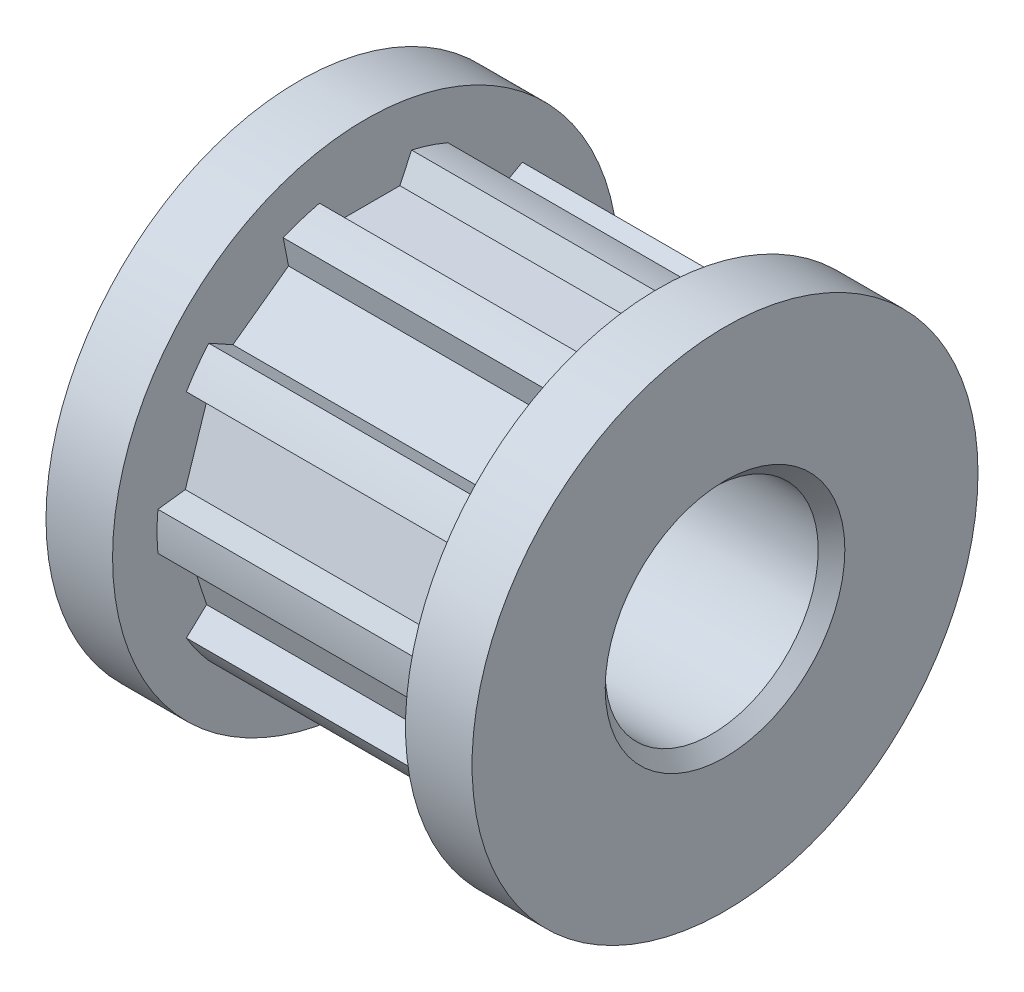
SolidWorks part; units mm, degrees
material "6061 合金"
ref_plane "前视基准面" through (0, 0, 0) normal (0, 0, 1) x (1, 0, 0)
ref_plane "上视基准面" through (0, 0, 0) normal (0, 1, 0) x (1, 0, 0)
ref_plane "右视基准面" through (0, 0, 0) normal (1, 0, 0) x (0, 0, -1)
sketch "草图1" plane through (0, 0, 0) normal (1, 0, 0) x (0, 0, -1)
  line L0 (0, 0) -> (0, 19.2746) construction
  line L22 (0, 0) -> (7.6303, 23.4837) construction
  line L89 (1.7283, 7.6369) -> (1.29, 6.6969)
  line L90 (0, 6.6969) -> (1.29, 6.6969)
  line L91 (3.0906, 7.1942) -> (2.8927, 6.1761)
  line L92 (3.9363, 5.4179) -> (2.8927, 6.1761)
  line L93 (6.729, 4.0037) -> (5.9705, 3.2963)
  line L94 (6.3691, 2.0695) -> (5.9705, 3.2963)
  line L95 (3.9363, 5.4179) -> (4.98, 4.6597)
  line L96 (5.8871, 5.1625) -> (4.98, 4.6597)
  line L97 (7.7972, -0.7162) -> (6.7678, -0.8426)
  line L98 (6.3691, -2.0695) -> (6.7678, -0.8426)
  line L99 (6.3691, 2.0695) -> (6.7678, 0.8426)
  line L100 (7.7972, 0.7162) -> (6.7678, 0.8426)
  line L101 (5.8871, -5.1625) -> (4.98, -4.6597)
  line L102 (3.9363, -5.4179) -> (4.98, -4.6597)
  line L103 (6.3691, -2.0695) -> (5.9705, -3.2963)
  line L104 (6.729, -4.0037) -> (5.9705, -3.2963)
  line L105 (1.7283, -7.6369) -> (1.29, -6.6969)
  line L106 (0, -6.6969) -> (1.29, -6.6969)
  line L107 (3.9363, -5.4179) -> (2.8927, -6.1761)
  line L108 (3.0906, -7.1942) -> (2.8927, -6.1761)
  line L109 (-3.0906, -7.1942) -> (-2.8927, -6.1761)
  line L110 (-3.9363, -5.4179) -> (-2.8927, -6.1761)
  line L111 (0, -6.6969) -> (-1.29, -6.6969)
  line L112 (-1.7283, -7.6369) -> (-1.29, -6.6969)
  line L113 (-6.729, -4.0037) -> (-5.9705, -3.2963)
  line L114 (-6.3691, -2.0695) -> (-5.9705, -3.2963)
  line L115 (-3.9363, -5.4179) -> (-4.98, -4.6597)
  line L116 (-5.8871, -5.1625) -> (-4.98, -4.6597)
  line L117 (-7.7972, 0.7162) -> (-6.7678, 0.8426)
  line L118 (-6.3691, 2.0695) -> (-6.7678, 0.8426)
  line L119 (-6.3691, -2.0695) -> (-6.7678, -0.8426)
  line L120 (-7.7972, -0.7162) -> (-6.7678, -0.8426)
  line L121 (-5.8871, 5.1625) -> (-4.98, 4.6597)
  line L122 (-3.9363, 5.4179) -> (-4.98, 4.6597)
  line L123 (-6.3691, 2.0695) -> (-5.9705, 3.2963)
  line L124 (-6.729, 4.0037) -> (-5.9705, 3.2963)
  line L125 (-1.7283, 7.6369) -> (-1.29, 6.6969)
  line L126 (0, 6.6969) -> (-1.29, 6.6969)
  line L127 (-3.9363, 5.4179) -> (-2.8927, 6.1761)
  line L128 (-3.0906, 7.1942) -> (-2.8927, 6.1761)
  arc A3 (3.0906, 7.1942) -> (1.7283, 7.6369) centre (0, 0) ccw
  arc A8 (6.729, 4.0037) -> (5.8871, 5.1625) centre (0, 0) ccw
  arc A9 (7.7972, -0.7162) -> (7.7972, 0.7162) centre (0, 0) ccw
  arc A10 (5.8871, -5.1625) -> (6.729, -4.0037) centre (0, 0) ccw
  arc A11 (1.7283, -7.6369) -> (3.0906, -7.1942) centre (0, 0) ccw
  arc A12 (-3.0906, -7.1942) -> (-1.7283, -7.6369) centre (0, 0) ccw
  arc A13 (-6.729, -4.0037) -> (-5.8871, -5.1625) centre (0, 0) ccw
  arc A14 (-7.7972, 0.7162) -> (-7.7972, -0.7162) centre (0, 0) ccw
  arc A15 (-5.8871, 5.1625) -> (-6.729, 4.0037) centre (0, 0) ccw
  arc A16 (-1.7283, 7.6369) -> (-3.0906, 7.1942) centre (0, 0) ccw
  circle A17 centre (0, 0) radius 4
  point P32 (0, 14.645)
  dimension "D1" = 18
  dimension "D2" = 7.83
  dimension "D4" = 6.82
  dimension "D3" = 10
  dimension "D7" = 8
  dimension "D5" = 115
  dimension "D6" = 1.29
extrude "凸台-拉伸1" add sketch "草图1" along normal blind 11
sketch "草图2" plane through (11, 0, 0) normal (1, 0, 0) x (0, 0, -1)
  circle A0 centre (0, 0) radius 9.5
  circle A1 centre (0, 0) radius 4
  point P4 (0, 0)
  dimension "D1" = 19
  dimension "D2" = 8
extrude "凸台-拉伸2" add sketch "草图2" along normal blind 2.5
sketch "草图3" plane through (0, 0, 0) normal (-1, 0, 0) x (0, 0, 1)
  circle A0 centre (0, 0) radius 4
  circle A1 centre (0, 0) radius 9.5
  point P4 (0, 0)
  point P5 (0, 0)
  dimension "D1" = 19
  dimension "D2" = 8
extrude "凸台-拉伸3" add sketch "草图3" along normal blind 2.5
chamfer "倒角1" distance 0.5 angle 45 2 edges at (13.5, 0, -4) (-2.5, 0, 4)
